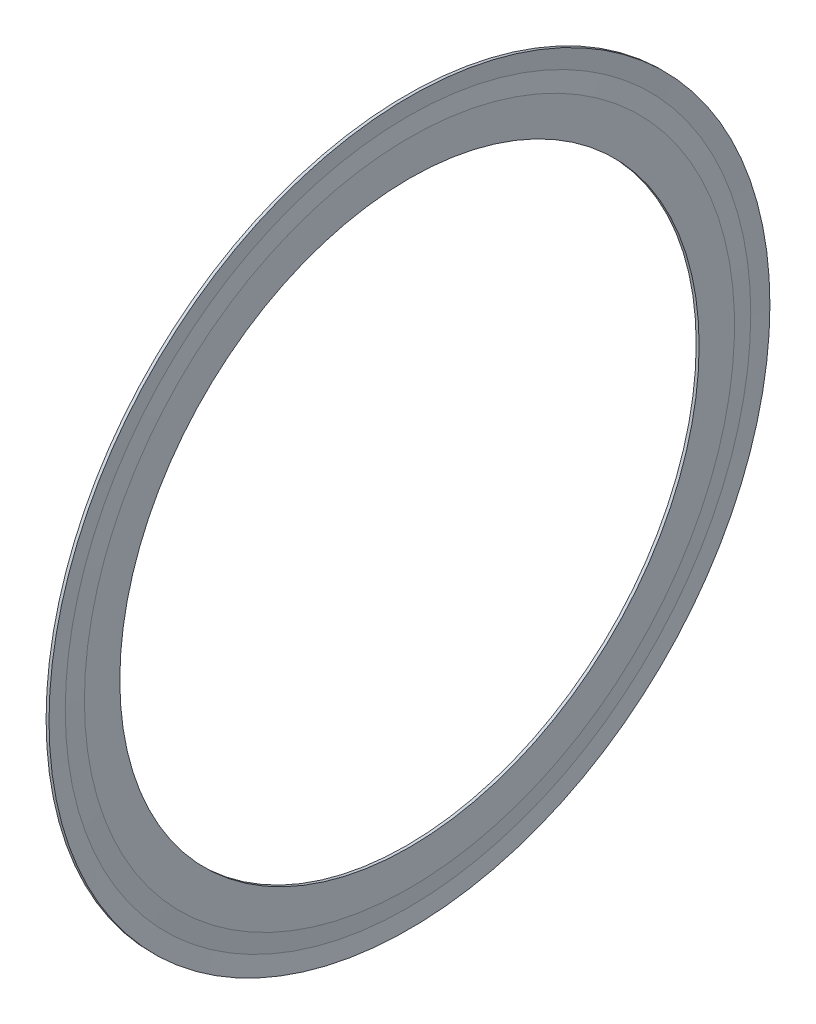
SolidWorks part; units mm, degrees
material "普通碳钢"
ref_plane "前视基准面" through (0, 0, 0) normal (0, 0, 1) x (1, 0, 0)
ref_plane "上视基准面" through (0, 0, 0) normal (0, 1, 0) x (1, 0, 0)
ref_plane "右视基准面" through (0, 0, 0) normal (1, 0, 0) x (0, 0, -1)
ref_plane "基准面1" through (0, 0, 0) normal (0, 0, 1) x (1, 0, 0)
sketch "草图1" plane through (0, 0, 0) normal (0, 0, 1) x (1, 0, 0)
  line L0 (4.55, 10.5312) -> (4.55, 9.9875)
  line L1 (4.55, 9.9875) -> (4.64, 8.9)
  line L2 (4.64, 8.9) -> (4.73, 8.9)
  line L3 (4.73, 8.9) -> (4.73, 9.9875)
  line L4 (4.73, 9.9875) -> (4.685, 10.5312)
  line L5 (4.685, 10.5312) -> (4.73, 11.075)
  line L6 (4.73, 11.075) -> (4.64, 11.075)
  line L7 (4.64, 11.075) -> (4.55, 10.5312)
  line L8 (50, 0) -> (-50, 0) construction
revolve "旋转1" add sketch "草图1" angle 360 about L8
